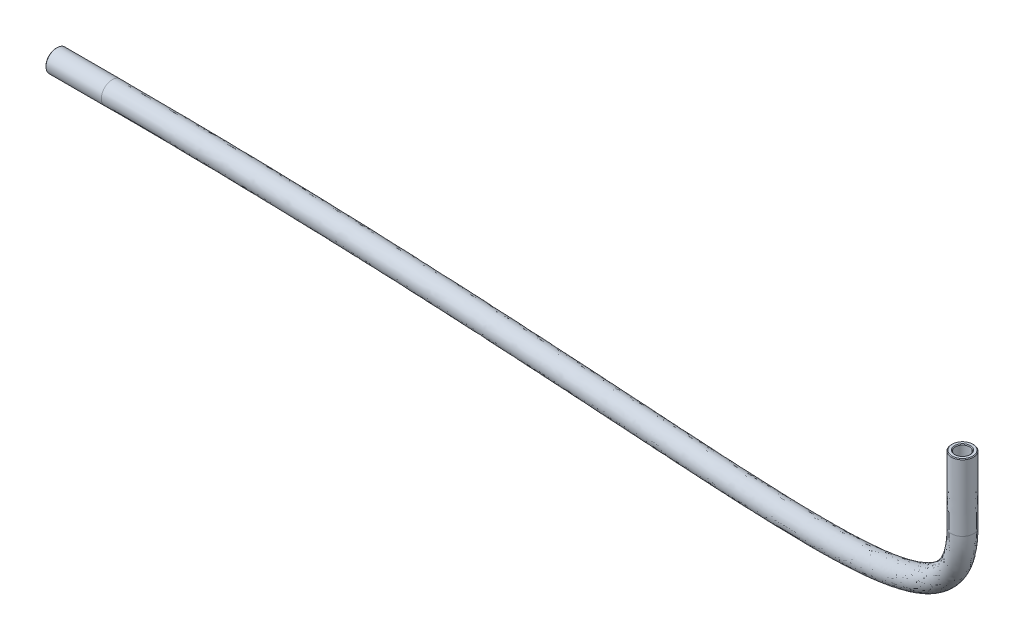
SolidWorks part; units mm, degrees
ref_plane "Front Plane" through (0, 0, 0) normal (0, 0, 1) x (1, 0, 0)
ref_plane "Top Plane" through (0, 0, 0) normal (0, 1, 0) x (1, 0, 0)
ref_plane "Right Plane" through (0, 0, 0) normal (1, 0, 0) x (0, 0, -1)
sketch3d "3DSketch1"
  line L0 (41.325, -62.125, 13.85) -> (41.325, -74.325, 13.85)
  line L1 (-136.8853, -106.4823, -9.525) -> (-147.0853, -106.4823, -9.525)
  spline S0 degree 3 poles (41.325, -74.325, 13.85) (41.325, -86.3464, 13.85) (9.9196, -103.3388, 2.1625) (-78.1566, -106.4823, -9.525) (-136.8853, -106.4823, -9.525) knots 0 0 0 0 0.478107 1 1 1 1
sketch "Sketch1" plane through (-138.9853, 0, 0) normal (1, 0, 0) x (0, 0, -1)
  circle A0 centre (9.525, -106.4823) radius 2
  circle A1 centre (9.525, -106.4823) radius 1.3
  circle A2 centre (9.525, -106.4823) radius 3.5 construction
  dimension "D1" = 2.6
  dimension "D2" = 4
sweep "Sweep1" add profiles "Sketch1" path "3DSketch1"
chamfer "Chamfer1" distance 0.127 angle 45 4 edges at (-147.0853, -104.4823, -9.525) (-147.0853, -105.1823, -9.525) (39.9324, -62.125, 12.4145) (40.4198, -62.125, 12.9169)
